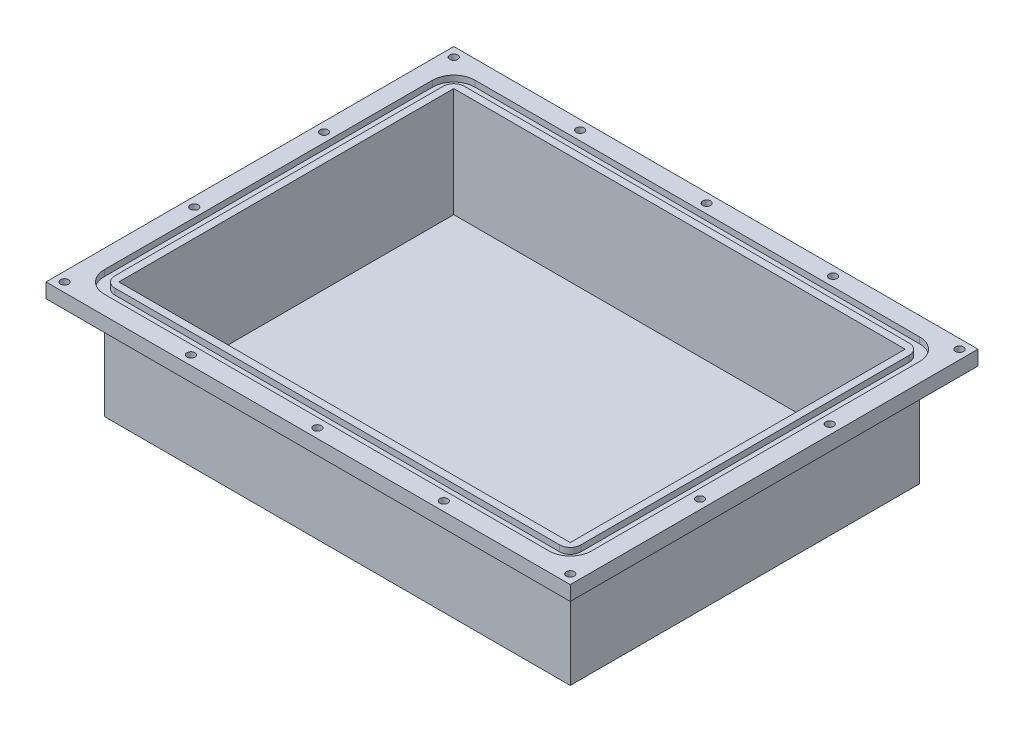
SolidWorks part; units mm, degrees
material "1060 Alloy"
ref_plane "Front Plane" through (0, 0, 0) normal (0, 0, 1) x (1, 0, 0)
ref_plane "Top Plane" through (0, 0, 0) normal (0, 1, 0) x (1, 0, 0)
ref_plane "Right Plane" through (0, 0, 0) normal (1, 0, 0) x (0, 0, -1)
sketch "Sketch1" plane through (0, 0, 0) normal (0, 1, 0) x (1, 0, 0)
  line L1 (101.6, -76.2) -> (-101.6, -76.2)
  line L2 (101.6, -76.2) -> (101.6, 76.2)
  line L3 (101.6, 76.2) -> (-101.6, 76.2)
  line L4 (-101.6, -76.2) -> (-101.6, 76.2)
  line L5 (101.6, -76.2) -> (-101.6, 76.2) construction
  line L6 (101.6, 76.2) -> (-101.6, -76.2) construction
  point P0 (0, 0)
  dimension "D1" = 152.4
  dimension "D2" = 203.2
extrude "Boss-Extrude1" add sketch "Sketch1" along normal blind 50.8
sketch "Sketch2" plane through (0, 50.8, 0) normal (0, 1, 0) x (1, 0, 0)
  line L8 (-98.425, 73.025) -> (-98.425, -73.025)
  line L9 (98.425, 73.025) -> (-98.425, 73.025)
  line L10 (98.425, -73.025) -> (98.425, 73.025)
  line L11 (-98.425, -73.025) -> (98.425, -73.025)
  line L12 (-98.425, 73.025) -> (-98.425, -73.025)
  line L13 (98.425, 73.025) -> (-98.425, 73.025)
  line L14 (98.425, -73.025) -> (98.425, 73.025)
  line L15 (-98.425, -73.025) -> (98.425, -73.025)
  dimension "D1" = 3.175
extrude "Cut-Extrude1" cut sketch "Sketch2" against normal offset from surface (47.625 mm away) 3.175 up to face at (0, 0, 0)
sketch "Sketch4" plane through (0, 50.8, 0) normal (0, 1, 0) x (1, 0, 0)
  line L0 (-101.6, 76.2) -> (-101.6, -76.2)
  line L1 (-101.6, -76.2) -> (101.6, -76.2)
  line L2 (101.6, -76.2) -> (101.6, 76.2)
  line L3 (101.6, 76.2) -> (-101.6, 76.2)
  line L4 (114.3, 88.9) -> (-114.3, 88.9)
  line L5 (-114.3, 88.9) -> (-114.3, -88.9)
  line L6 (-114.3, -88.9) -> (114.3, -88.9)
  line L7 (114.3, -88.9) -> (114.3, 88.9)
  dimension "D1" = 12.7
extrude "Boss-Extrude2" add sketch "Sketch4" against normal blind 6.35
sketch "Sketch7" plane through (0, 50.8, 0) normal (0, 1, 0) x (1, 0, 0)
  line L4 (-106.2228, 80.8228) -> (-106.2228, -80.8228)
  line L5 (-106.2228, -80.8228) -> (106.2228, -80.8228)
  line L6 (106.2228, -80.8228) -> (106.2228, 80.8228)
  line L7 (106.2228, 80.8228) -> (-106.2228, 80.8228)
  line L8 (-101.6, -76.2) -> (101.6, -76.2)
  line L9 (101.6, -76.2) -> (101.6, 76.2)
  line L10 (101.6, 76.2) -> (-101.6, 76.2)
  line L11 (-101.6, 76.2) -> (-101.6, -76.2)
  line L12 (-101.6, -76.2) -> (101.6, -76.2)
  line L13 (101.6, -76.2) -> (101.6, 76.2)
  line L14 (101.6, 76.2) -> (-101.6, 76.2)
  line L15 (-101.6, 76.2) -> (-101.6, -76.2)
  dimension "D1" = 3.175
  dimension "D2" = 4.6228
extrude "Cut-Extrude2" cut sketch "Sketch7" against normal blind 2.6416
hole_wizard "#8-32 Tapped Hole1" positions "Sketch6" profile "Sketch5" tap size "#8-32" standard "ANSI Inch" end condition through all
sketch "Sketch6" plane through (0, 50.8, 0) normal (0, 1, 0) x (1, 0, 0)
  line L0 (0, 0) -> (0, 88.9) construction
  line L1 (114.3, 88.9) -> (-114.3, 88.9) construction
  line L4 (0, 0) -> (114.3, 0) construction
  line L5 (114.3, -88.9) -> (114.3, 88.9) construction
  line L6 (0, 84.8614) -> (55.1307, 84.8614) construction
  line L7 (55.1307, 84.8614) -> (110.2614, 84.8614) construction
  line L10 (110.2614, 84.8614) -> (110.2614, 28.2871) construction
  line L13 (110.2614, 28.2871) -> (110.2614, -28.2871) construction
  line L16 (106.2228, 80.8228) -> (114.3, 88.9) construction
  point P22 (55.1307, 84.8614)
  point P24 (110.2614, 84.8614)
  point P26 (110.2614, 28.2871)
  point P110 (0, 84.8614)
  point P132 (110.2614, -28.2871)
  point P133 (110.2614, -84.8614)
  point P134 (55.1307, -84.8614)
  point P135 (0, -84.8614)
  point P145 (-55.1307, -84.8614)
  point P146 (-110.2614, -84.8614)
  point P147 (-110.2614, -28.2871)
  point P148 (-110.2614, 28.2871)
  point P149 (-110.2614, 84.8614)
  point P150 (-55.1307, 84.8614)
sketch "Sketch5" plane through (55.1307, 50.8, -84.8614) normal (1, 0, 0) x (0, 0, 1)
  line L0 (0, 0) -> (0, 50.8)
  line L1 (0, 50.8) -> (1.7272, 50.8)
  line L2 (1.7272, 50.8) -> (1.7272, 0)
  line L5 (1.7272, 0) -> (0, 0)
  line L11 (0, -6.35) -> (0, 107.95) construction
  dimension "Thread Major Dia." = 3.4544
  dimension "Thru Tap Drill Depth" = 50.8
sketch "O Ring Corner Fillet Dimentions" plane through (0, 50.8, 0) normal (0, 1, 0) x (1, 0, 0)
  line L0 (106.2228, 80.8228) -> (96.9772, 71.5772) construction
  line L1 (106.2228, 80.8228) -> (-106.2228, 80.8228) construction
  line L2 (106.2228, -80.8228) -> (106.2228, 80.8228) construction
  circle A0 centre (96.9772, 71.5772) radius 9.2456
  circle A1 centre (96.9772, 71.5772) radius 4.6228
  dimension "D1" = 4.6228
  dimension "D2" = 18.4912
  dimension "D3" = 9.2456
fillet "Fillet3" radius 4.6228 4 edges at (101.6, 49.4792, 76.2) (-101.6, 49.4792, 76.2) (-101.6, 49.4792, -76.2) (101.6, 49.4792, -76.2)
fillet "Fillet4" radius 9.2456 4 edges at (106.2228, 49.4792, 80.8228) (-106.2228, 49.4792, 80.8228) (-106.2228, 49.4792, -80.8228) (106.2228, 49.4792, -80.8228)
